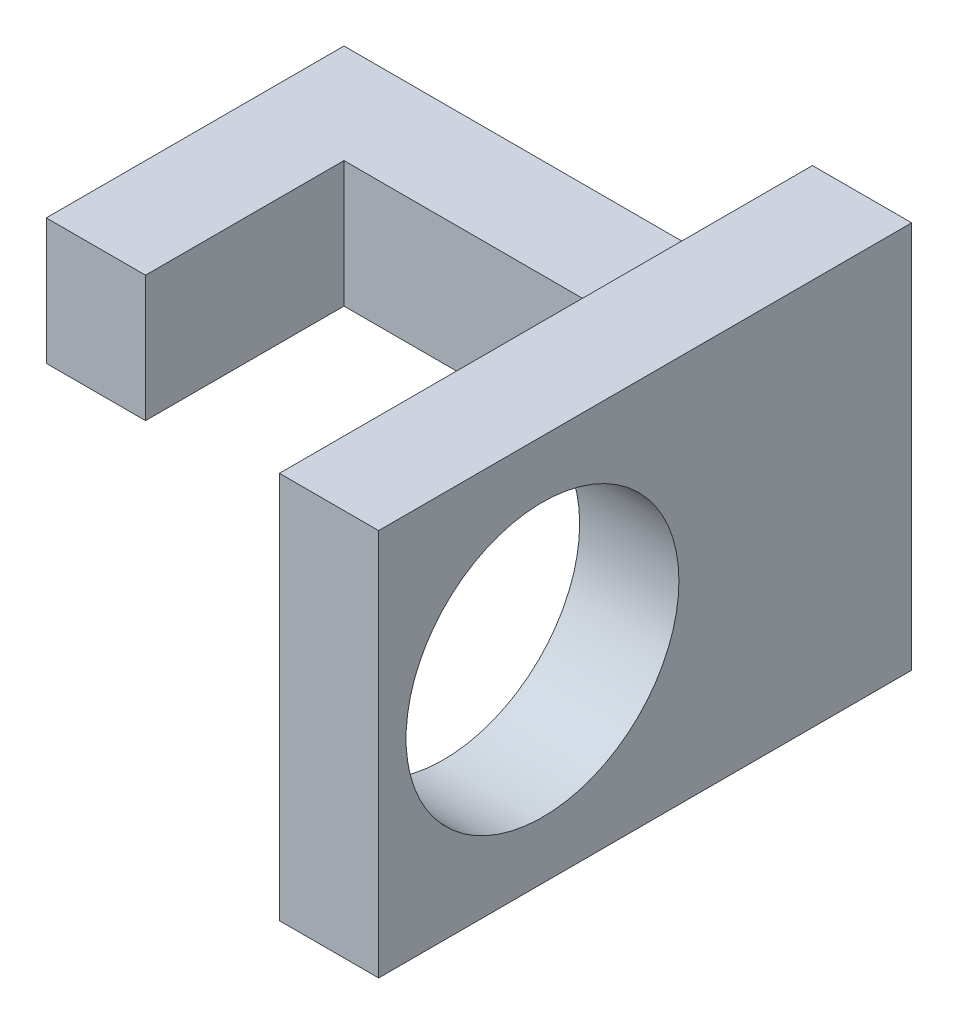
SolidWorks part; units mm, degrees
ref_plane "Front Plane" through (0, 0, 0) normal (0, 0, 1) x (1, 0, 0)
ref_plane "Top Plane" through (0, 0, 0) normal (0, 1, 0) x (1, 0, 0)
ref_plane "Right Plane" through (0, 0, 0) normal (1, 0, 0) x (0, 0, -1)
sketch "Sketch1" plane through (0, 0, 0) normal (0, 1, 0) x (1, 0, 0)
  line L2 (-24.2639, 4.8561) -> (-24.2639, -1.1439)
  line L3 (-24.2639, -1.1439) -> (-22.2639, -1.1439)
  line L4 (-22.2639, 2.8561) -> (-22.2639, -1.1439)
  line L5 (-22.2639, 2.8561) -> (-14.8217, 2.8561)
  line L7 (-24.2639, 4.8561) -> (-14.8217, 4.8561)
  line L8 (-14.8217, 2.8561) -> (-14.8217, 4.8561)
  dimension "D1" = 2
  dimension "D2" = 7.4422
  dimension "D3" = 4
  dimension "D4" = 2
extrude "Boss-Extrude1" add sketch "Sketch1" along normal blind 2.54
sketch3d "3DSketch1"
  line L1 (-14.8217, 5.1747, 5.8876) -> (-14.8217, -2.6347, 5.8876)
  line L2 (-14.8217, 5.1747, 5.8876) -> (-14.8217, 5.1747, -4.8561)
  line L3 (-14.8217, 5.1747, -4.8561) -> (-14.8217, -2.6347, -4.8561)
  line L4 (-14.8217, -2.6347, 5.8876) -> (-14.8217, -2.6347, -4.8561)
  line L5 (-14.8217, 2.54, -4.8561) -> (-14.8217, 0, -4.8561) construction
  line L6 (-14.8217, 1.27, 5.8876) -> (-14.8217, 1.27, -4.8561) construction
  line L7 (-22.2639, 2.54, -2.8561) -> (-14.8217, 2.54, -2.8561) construction
  circle A0 centre (-14.8217, 1.27, 2.5856) radius 2.75
  point P6 (-12.0717, 1.27, 2.5856)
  point P12 (-14.8217, 1.27, -4.8561)
  point P13 (-14.8217, 1.27, -4.8561)
  dimension "D3" = 5.5
  dimension "D2" = 3.302
  dimension "D4" = 5.588
extrude "Boss-Extrude3" add sketch "3DSketch1" along direction (-1, 0, 0) on the side of the normal blind 2
